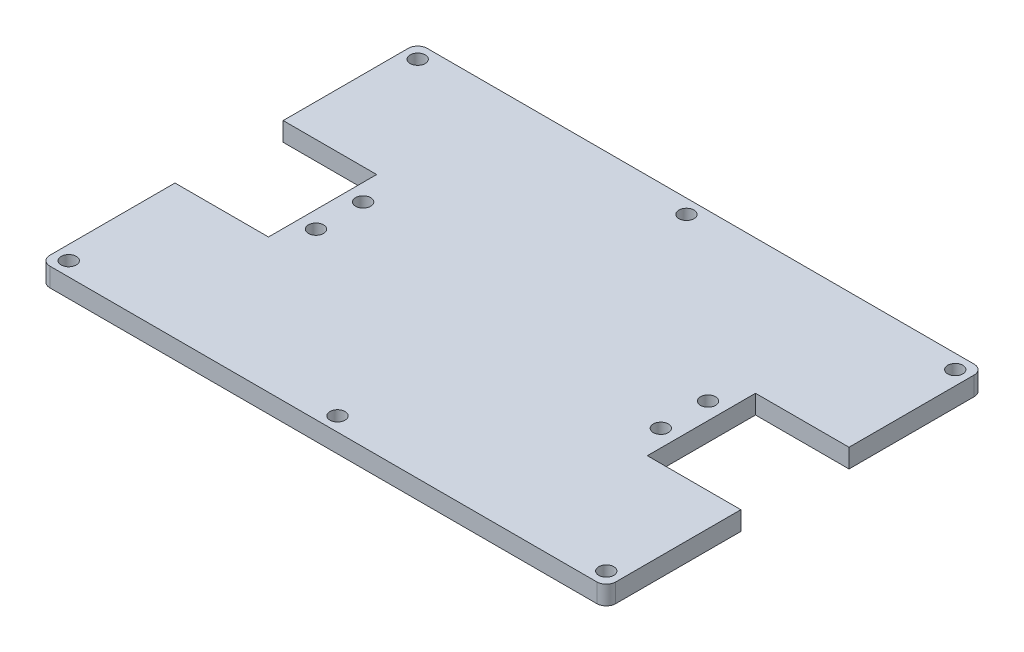
SolidWorks part; units mm, degrees
ref_plane "Front Plane" through (0, 0, 0) normal (0, 0, 1) x (1, 0, 0)
ref_plane "Top Plane" through (0, 0, 0) normal (0, 1, 0) x (1, 0, 0)
ref_plane "Right Plane" through (0, 0, 0) normal (1, 0, 0) x (0, 0, -1)
sketch "Sketch2" plane through (0, 0, 0) normal (0, 1, 0) x (1, 0, 0)
  line L0 (0, 40) -> (120, 40) construction
  line L1 (0, 0) -> (120, 0)
  line L2 (0, 0) -> (0, 80)
  line L3 (0, 80) -> (120, 80)
  line L4 (120, 0) -> (120, 80)
  line L5 (0, 40) -> (0, 51.47)
  line L6 (0, 51.47) -> (19.83, 51.47)
  line L7 (19.83, 51.47) -> (19.83, 28.53)
  line L8 (19.83, 28.53) -> (0, 28.53)
  line L9 (0, 28.53) -> (0, 40)
  line L10 (3, 80) -> (3, 77) construction
  line L11 (120, 51.47) -> (100.17, 51.47)
  line L12 (120, 51.47) -> (120, 28.53)
  line L13 (120, 28.53) -> (100.17, 28.53)
  line L14 (100.17, 51.47) -> (100.17, 28.53)
  line L15 (3, 77) -> (0, 77) construction
  line L16 (0, 77) -> (3, 77) construction
  line L17 (0, 3) -> (3, 3) construction
  line L18 (3, 3) -> (3, 0) construction
  line L19 (117, 80) -> (117, 77) construction
  line L20 (117, 77) -> (120, 77) construction
  line L21 (117, 0) -> (117, 3) construction
  line L22 (117, 3) -> (120, 3) construction
  line L23 (23.43, 40) -> (23.43, 45) construction
  line L24 (23.43, 40) -> (23.43, 35) construction
  line L25 (96.57, 40) -> (96.57, 45) construction
  line L26 (96.57, 40) -> (96.57, 35) construction
  line L27 (60, 80) -> (60, 0) construction
  circle A0 centre (3, 77) radius 1.6
  circle A1 centre (3, 3) radius 1.6
  circle A2 centre (117, 77) radius 1.6
  circle A3 centre (117, 3) radius 1.6
  circle A4 centre (23.43, 45) radius 1.6
  circle A5 centre (23.43, 35) radius 1.6
  circle A6 centre (96.57, 45) radius 1.6
  circle A7 centre (96.57, 35) radius 1.6
  circle A8 centre (60, 77) radius 1.6
  circle A9 centre (60, 3) radius 1.6
  point P32 (19.83, 40)
  point P33 (100.17, 40)
  dimension "D11" = 3.2
  dimension "D14" = 3.2
  dimension "D17" = 3.2
  dimension "D20" = 3.2
  dimension "D21" = 3.2
  dimension "D23" = 3.2
  dimension "D25" = 3.2
  dimension "D28" = 3.2
  dimension "D30" = 3.2
  dimension "D32" = 3.2
  dimension "D1" = 80
  dimension "D2" = 120
  dimension "D3" = 22.94
  dimension "D4" = 5
  dimension "D5" = 19.83
  dimension "D6" = 19.83
  dimension "D7" = 22.94
  dimension "D8" = 3.6
  dimension "D9" = 3
  dimension "D10" = 3
  dimension "D12" = 3
  dimension "D13" = 3
  dimension "D15" = 3
  dimension "D16" = 3
  dimension "D18" = 3
  dimension "D19" = 3
  dimension "D22" = 5
  dimension "D24" = 5
  dimension "D26" = 3.6
  dimension "D27" = 5
  dimension "D29" = 3
  dimension "D31" = 3
extrude "Boss-Extrude2" add sketch "Sketch2" along normal blind 4 contours L14 L11 L4 L3 L2 L6 L7 L8 L1 L13 A9 A8 A7 A6 A5 A4 A3 A2 A1 A0
fillet "Fillet1" radius 2 1 edges at (0, 2, -80)
fillet "Fillet2" radius 2 1 edges at (120, 2, -80)
fillet "Fillet3" radius 2 1 edges at (120, 2, 0)
fillet "Fillet4" radius 2 1 edges at (0, 2, 0)
